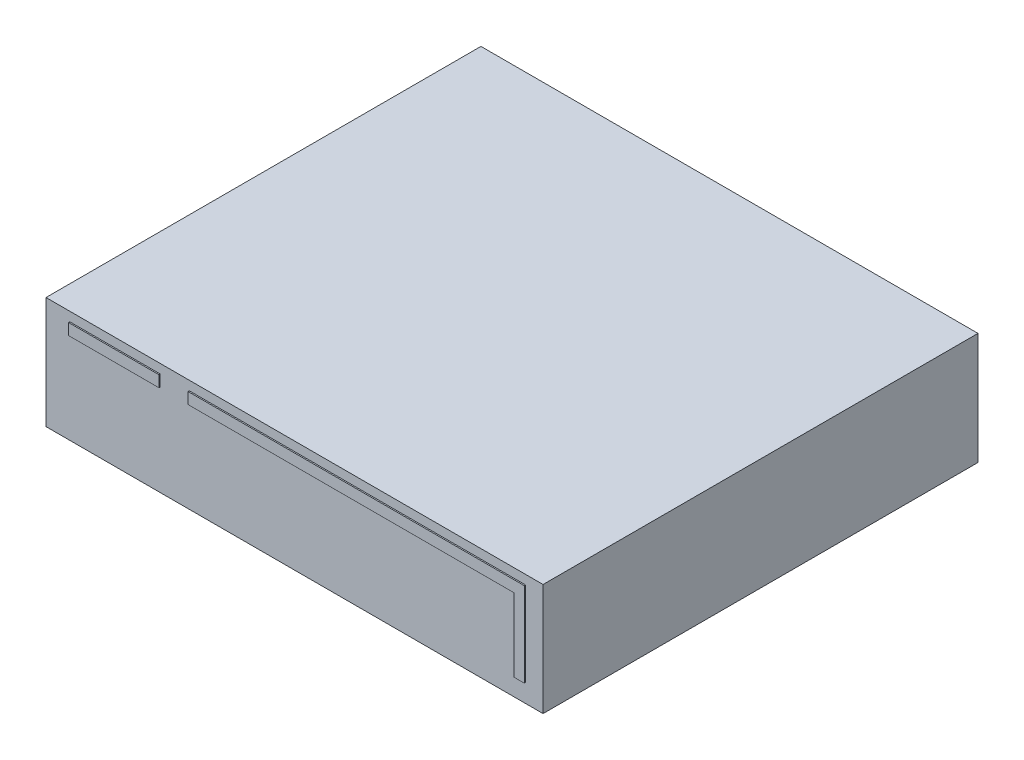
SolidWorks part; units mm, degrees
ref_plane "Alzado" through (0, 0, 0) normal (0, 0, 1) x (1, 0, 0)
ref_plane "Planta" through (0, 0, 0) normal (0, 1, 0) x (1, 0, 0)
ref_plane "Vista lateral" through (0, 0, 0) normal (1, 0, 0) x (0, 0, -1)
sketch "Croquis1" plane through (0, 0, 0) normal (0, 0, 1) x (1, 0, 0)
  line L1 (-200, 45) -> (200, 45)
  line L2 (-200, 45) -> (-200, -45)
  line L3 (-200, -45) -> (200, -45)
  line L4 (200, 45) -> (200, -45)
  line L5 (-200, 45) -> (200, -45) construction
  line L6 (-200, -45) -> (200, 45) construction
  point P0 (0, 0)
  dimension "D1" = 400
  dimension "D2" = 90
extrude "Saliente-Extruir1" add sketch "Croquis1" against normal blind 350
sketch "Croquis2" plane through (0, 0, 0) normal (0, 0, 1) x (1, 0, 0)
  line L1 (-180.7739, 37.6252) -> (-108.1184, 37.6252)
  line L2 (-180.7739, 37.6252) -> (-180.7739, 28.5432)
  line L3 (-180.7739, 28.5432) -> (-108.1184, 28.5432)
  line L4 (-108.1184, 37.6252) -> (-108.1184, 28.5432)
  line L5 (-84.7648, 37.6252) -> (185.9636, 37.6252)
  line L6 (-84.7648, 37.6252) -> (-84.7648, 28.5432)
  line L7 (-84.7648, 28.5432) -> (177.5033, 28.5432)
  line L8 (185.9636, 37.6252) -> (185.9636, 28.5432)
  line L10 (185.9636, 28.5432) -> (185.9636, -30.3335)
  line L11 (185.9636, -30.3335) -> (177.5033, -30.3335)
  line L12 (177.5033, 28.5432) -> (177.5033, -30.3335)
extrude "Saliente-Extruir2" add sketch "Croquis2" along normal blind 1
